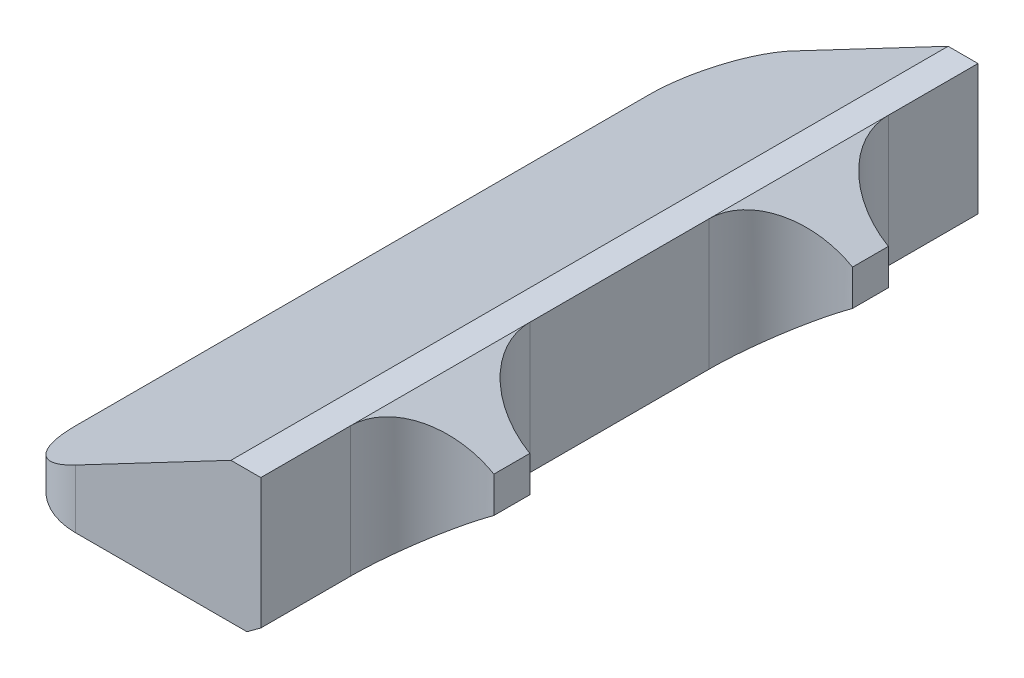
SolidWorks part; units mm, degrees
material "Fused silica"
ref_plane "Front Plane" through (0, 0, 0) normal (0, 0, 1) x (1, 0, 0)
ref_plane "Top Plane" through (0, 0, 0) normal (0, 1, 0) x (1, 0, 0)
ref_plane "Right Plane" through (0, 0, 0) normal (1, 0, 0) x (0, 0, -1)
sketch "Sketch1" plane through (0, 0, 0) normal (0, 0, 1) x (1, 0, 0)
  line L0 (0, 0) -> (20, 0)
  line L1 (20, 0) -> (27.5, 5.5)
  line L2 (27.5, 5.5) -> (27.5, 8.5)
  line L3 (19, 12) -> (21.5, 12)
  line L4 (19, 12) -> (0, 2)
  line L5 (0, 2) -> (0, 0)
  line L6 (21.5, 12) -> (27.5, 8.5)
  dimension "D1" = 20
  dimension "D2" = 2
  dimension "D3" = 12
  dimension "D4" = 3
  dimension "D5" = 7.5
  dimension "D6" = 6
  dimension "D7" = 2.5
  dimension "D8" = 5.5
  dimension "D9" = 27.759
  dimension "D10" = 30.256
  dimension "D11" = 36.254
extrude "Extrude1" add sketch "Sketch1" along normal blind 60
sketch "Sketch2" plane through (0, 0, 0) normal (0, 1, 0) x (1, 0, 0)
  line L0 (27.5, -13.5) -> (27.5, -16.5)
  line L2 (27.5, -43.5) -> (27.5, -46.5)
  line L4 (21.5, -22.5) -> (21.5, -37.5)
  line L5 (21.5, -52.5) -> (21.5, -60)
  line L6 (21.5, -60) -> (28.5, -60)
  line L7 (28.5, -60) -> (28.5, 0)
  line L8 (28.5, 0) -> (21.5, 0)
  line L9 (21.5, 0) -> (21.5, -7.5)
  line L10 (27.5, -13.5) -> (21.5, -13.5) construction
  line L11 (27.5, -15) -> (25.5, -15) construction
  line L12 (27.5, -16.5) -> (21.5, -16.5) construction
  line L13 (27.5, -43.5) -> (25.5, -43.5) construction
  line L14 (27.5, -45) -> (25.5, -45) construction
  line L15 (27.5, -46.5) -> (25.5, -46.5) construction
  line L16 (19, -60) -> (0, -60) construction
  line L17 (19, 0) -> (0, 0) construction
  line L18 (27.5, -60) -> (27.5, 0) construction
  arc A0 (27.5, -13.5) -> (21.5, -7.5) centre (27.5, -7.5) cw
  arc A1 (27.5, -16.5) -> (21.5, -22.5) centre (27.5, -22.5) ccw
  arc A2 (27.5, -43.5) -> (21.5, -37.5) centre (27.5, -37.5) cw
  arc A3 (27.5, -46.5) -> (21.5, -52.5) centre (27.5, -52.5) ccw
  dimension "D2" = 7
  dimension "D1" = 3
  dimension "D3" = 30
  dimension "D4" = 1
extrude "Cut-Extrude1" cut sketch "Sketch2" along normal through all
fillet "Fillet1" radius 6 2 edges at (0, 1, 0) (0, 1, 60)
chamfer "Chamfer1" distance 0.25 angle 45 5 edges at (13, 0, 0) (1.7574, 0, 1.7574) (0, 0, 30) (1.7574, 0, 58.2426) (13, 0, 60)
fillet "Fillet2" [suppressed] radius 0.5
fillet "Fillet3" [suppressed] radius 0.2
